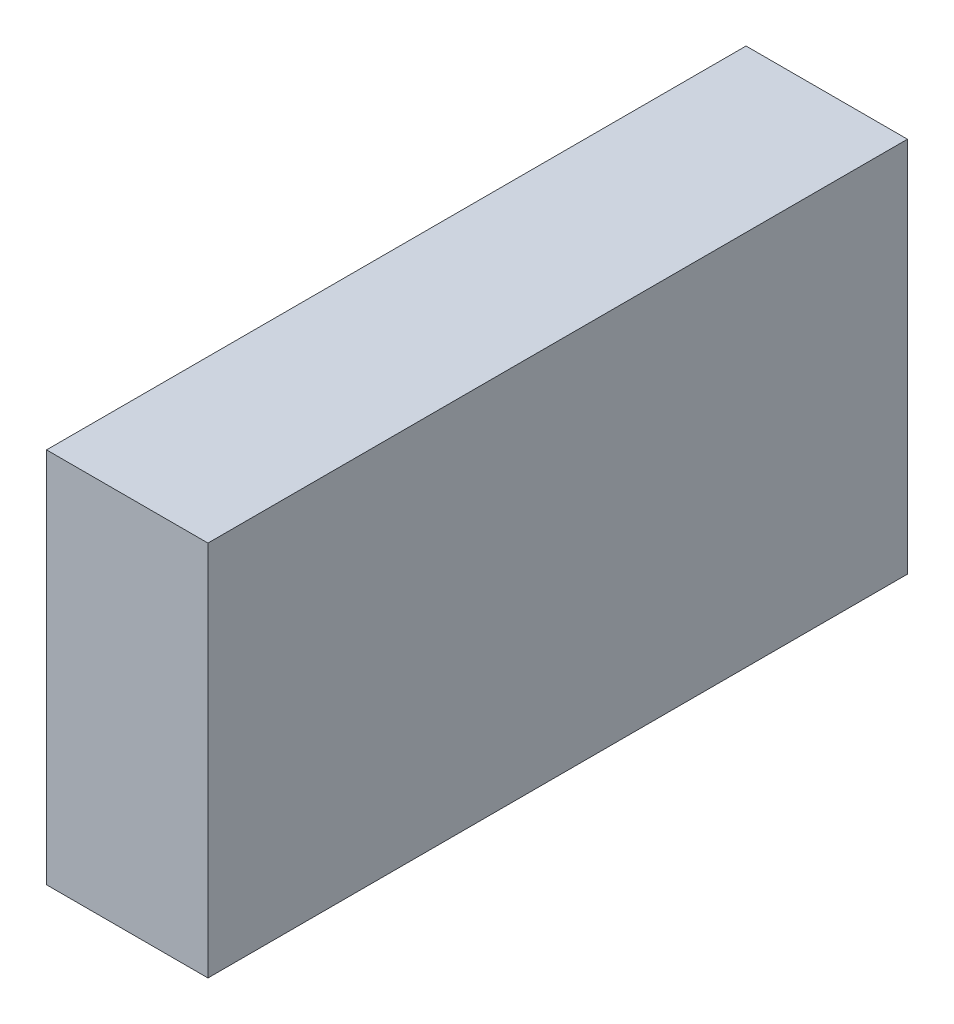
SolidWorks part; units mm, degrees
ref_plane "Front Plane" through (0, 0, 0) normal (0, 0, 1) x (1, 0, 0)
ref_plane "Top Plane" through (0, 0, 0) normal (0, 1, 0) x (1, 0, 0)
ref_plane "Right Plane" through (0, 0, 0) normal (1, 0, 0) x (0, 0, -1)
sketch "Sketch1" plane through (0, 0, 0) normal (0, 0, 1) x (1, 0, 0)
  line L1 (19.05, -44.45) -> (-19.05, -44.45)
  line L2 (19.05, -44.45) -> (19.05, 44.45)
  line L3 (19.05, 44.45) -> (-19.05, 44.45)
  line L4 (-19.05, -44.45) -> (-19.05, 44.45)
  line L5 (19.05, -44.45) -> (-19.05, 44.45) construction
  line L6 (19.05, 44.45) -> (-19.05, -44.45) construction
  point P0 (0, 0)
  dimension "D1" = 38.1
  dimension "D2" = 88.9
extrude "Boss-Extrude1" add sketch "Sketch1" along normal mid plane 165.1
